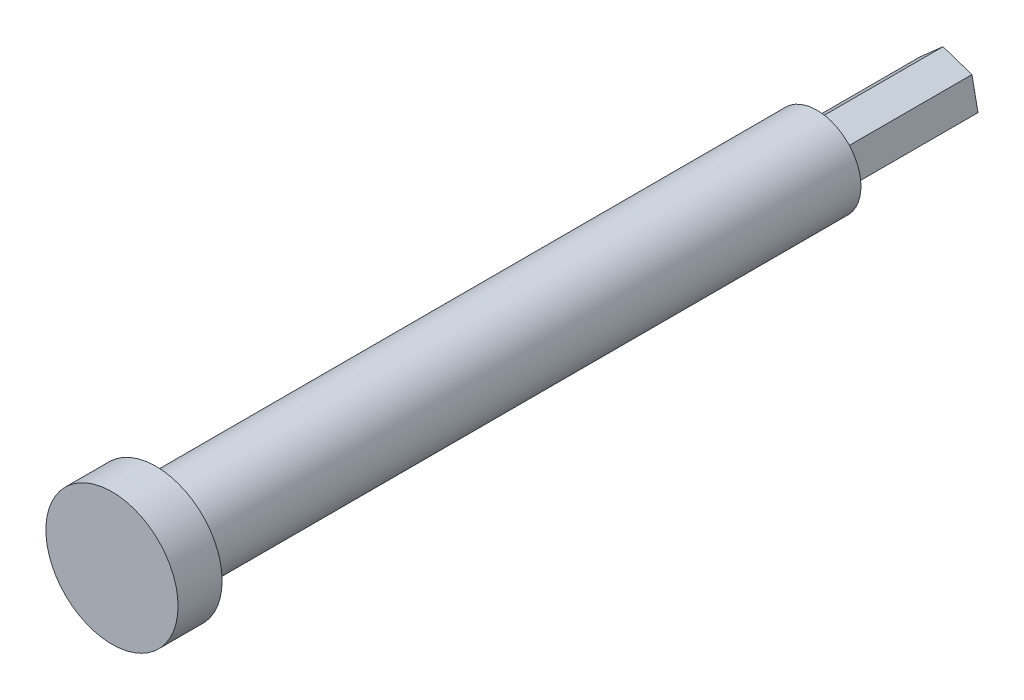
SolidWorks part; units mm, degrees
ref_plane "Plan de face" through (0, 0, 0) normal (0, 0, 1) x (1, 0, 0)
ref_plane "Plan de dessus" through (0, 0, 0) normal (0, 1, 0) x (1, 0, 0)
ref_plane "Plan de droite" through (0, 0, 0) normal (1, 0, 0) x (0, 0, -1)
sketch "Esquisse1" plane through (0, 0, 0) normal (0, 0, 1) x (1, 0, 0)
  line L1 (-0.6866, 3.3954) -> (-3.2838, 1.103)
  line L2 (-3.2838, 1.103) -> (-2.5971, -2.2923)
  line L3 (-2.5971, -2.2923) -> (0.6866, -3.3954)
  line L4 (0.6866, -3.3954) -> (3.2838, -1.103)
  line L5 (3.2838, -1.103) -> (2.5971, 2.2923)
  line L6 (2.5971, 2.2923) -> (-0.6866, 3.3954)
  circle A0 centre (0, 0) radius 3 construction
  dimension "D1" = 6
extrude "Boss.-Extru.1" add sketch "Esquisse1" along normal blind 15
sketch "Esquisse2" plane through (0, 0, 15) normal (0, 0, 1) x (1, 0, 0)
  circle A0 centre (0, 0) radius 5
  dimension "D1" = 10
extrude "Boss.-Extru.2" add sketch "Esquisse2" along normal blind 75
sketch "Esquisse3" plane through (0, 0, 90) normal (0, 0, 1) x (1, 0, 0)
  circle A0 centre (0, 0) radius 7.5
  dimension "D1" = 15
extrude "Boss.-Extru.3" add sketch "Esquisse3" along normal blind 5
